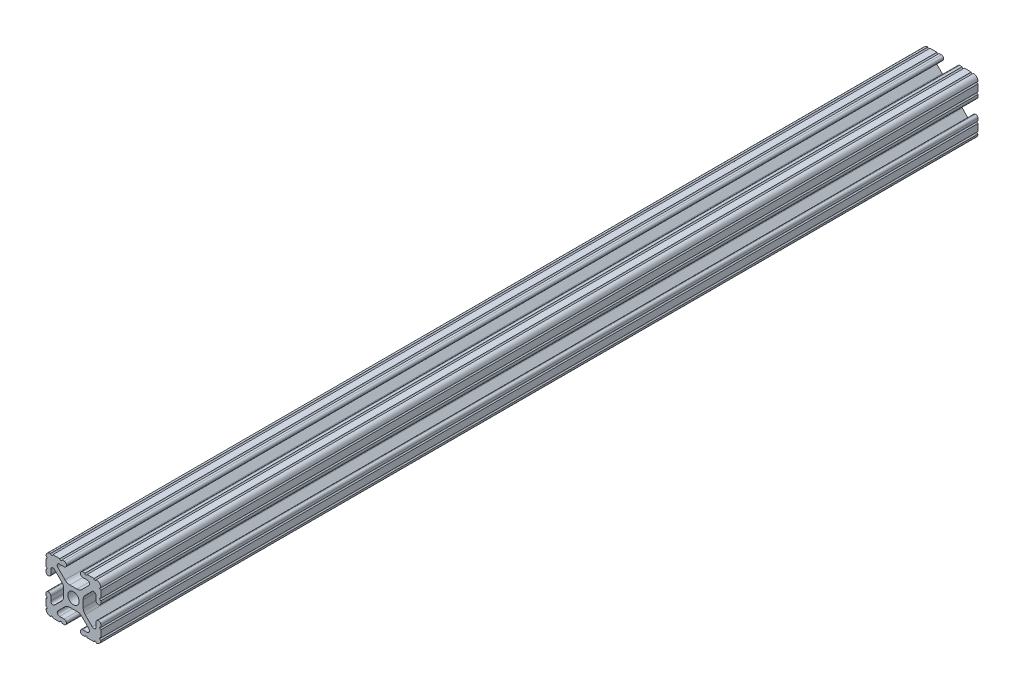
SolidWorks part; units mm, degrees
ref_plane "Front Plane" through (0, 0, 0) normal (0, 0, 1) x (1, 0, 0)
ref_plane "Top Plane" through (0, 0, 0) normal (0, 1, 0) x (1, 0, 0)
ref_plane "Right Plane" through (0, 0, 0) normal (1, 0, 0) x (0, 0, -1)
sketch "Sketch1" plane through (0, 0, 0) normal (0, 0, 1) x (1, 0, 0)
  line L0 (-7.207, 8.7244) -> (-3.8983, 5.4232)
  line L1 (-4.2875, 10.4902) -> (-6.4768, 10.4902)
  line L2 (-3.2385, 11.651) -> (-3.2385, 11.5392)
  line L3 (-5.3171, 12.7) -> (-4.2875, 12.7)
  line L4 (0, 13.4005) -> (0, -14.8534) construction
  line L5 (12.7, 0) -> (-13.9989, 0) construction
  line L6 (-9.5504, 12.7) -> (-6.3331, 12.7)
  line L7 (-12.7, 6.3331) -> (-12.7, 9.5504)
  line L8 (-12.7, 4.2875) -> (-12.7, 5.3171)
  line L9 (-11.5392, 3.2385) -> (-11.651, 3.2385)
  line L10 (-10.4902, 6.4021) -> (-10.4902, 4.2875)
  line L11 (-5.441, 3.8408) -> (-8.7371, 7.1294)
  line L12 (-4.5085, -1.5932) -> (-4.5085, 1.5932)
  line L13 (-1.7093, -4.4958) -> (1.7093, -4.4958)
  line L14 (3.9523, -5.4237) -> (7.1797, -8.6452)
  line L15 (6.4164, -10.4902) -> (4.2875, -10.4902)
  line L16 (3.2385, -11.5392) -> (3.2385, -11.651)
  line L17 (4.2875, -12.7) -> (5.3171, -12.7)
  line L18 (6.3331, -12.7) -> (9.5504, -12.7)
  line L19 (12.7, -9.5504) -> (12.7, -6.3331)
  line L20 (12.7, -5.3171) -> (12.7, -4.2875)
  line L21 (11.651, -3.2385) -> (11.5392, -3.2385)
  line L22 (10.4902, -4.2875) -> (10.4902, -6.4021)
  line L23 (8.7371, -7.1294) -> (5.441, -3.8408)
  line L24 (4.5085, -1.5932) -> (4.5085, 1.5932)
  line L25 (5.441, 3.8408) -> (8.7371, 7.1294)
  line L26 (10.4902, 6.4021) -> (10.4902, 4.2875)
  line L27 (11.5392, 3.2385) -> (11.651, 3.2385)
  line L28 (12.7, 4.2875) -> (12.7, 5.3171)
  line L29 (12.7, 6.3331) -> (12.7, 9.5504)
  line L30 (9.5504, 12.7) -> (6.3331, 12.7)
  line L31 (5.3171, 12.7) -> (4.2875, 12.7)
  line L32 (3.2385, 11.651) -> (3.2385, 11.5392)
  line L33 (4.2875, 10.4902) -> (6.4768, 10.4902)
  line L34 (7.207, 8.7244) -> (3.8983, 5.4232)
  line L35 (1.6558, 4.4958) -> (-1.6558, 4.4958)
  line L36 (-8.7371, -7.1294) -> (-5.441, -3.8408)
  line L37 (-10.4902, -4.2875) -> (-10.4902, -6.4021)
  line L38 (-11.651, -3.2385) -> (-11.5392, -3.2385)
  line L39 (-12.7, -5.3171) -> (-12.7, -4.2875)
  line L40 (-12.7, -9.5504) -> (-12.7, -6.3331)
  line L41 (-6.3331, -12.7) -> (-9.5504, -12.7)
  line L42 (-4.2875, -12.7) -> (-5.3171, -12.7)
  line L43 (-3.2385, -11.5392) -> (-3.2385, -11.651)
  line L44 (-6.4164, -10.4902) -> (-4.2875, -10.4902)
  line L45 (-3.9523, -5.4237) -> (-7.1797, -8.6452)
  arc A0 (-7.207, 8.7244) -> (-6.4768, 10.4902) centre (-6.4768, 9.4563) cw
  arc A1 (-3.2385, 11.5392) -> (-4.2875, 10.4902) centre (-4.2875, 11.5392) cw
  arc A2 (-4.2875, 12.7) -> (-3.2385, 11.651) centre (-4.2875, 11.651) cw
  arc A3 (-5.3171, 12.7) -> (-6.3331, 12.7) centre (-5.8251, 12.7) cw
  arc A4 (-9.5504, 12.7) -> (-10.5664, 12.6998) centre (-10.0584, 12.7) cw
  arc A5 (-12.6998, 10.5664) -> (-10.5664, 12.6998) centre (-10.5918, 10.5918) cw
  arc A6 (-12.6998, 10.5664) -> (-12.7, 9.5504) centre (-12.7, 10.0584) cw
  arc A7 (-12.7, 6.3331) -> (-12.7, 5.3171) centre (-12.7, 5.8251) cw
  arc A8 (-11.651, 3.2385) -> (-12.7, 4.2875) centre (-11.651, 4.2875) cw
  arc A9 (-10.4902, 4.2875) -> (-11.5392, 3.2385) centre (-11.5392, 4.2875) cw
  circle A10 centre (0, 0) radius 2.6035
  arc A11 (-10.4902, 6.4021) -> (-8.7371, 7.1294) centre (-9.4628, 6.4021) cw
  arc A12 (-5.441, 3.8408) -> (-4.5085, 1.5932) centre (-7.6835, 1.5932) cw
  arc A13 (-4.5085, -1.5932) -> (-5.441, -3.8408) centre (-7.6835, -1.5932) cw
  arc A14 (-8.7371, -7.1294) -> (-10.4902, -6.4021) centre (-9.4628, -6.4021) cw
  arc A15 (-1.7093, -4.4958) -> (-3.9523, -5.4237) centre (-1.7093, -7.6708) ccw
  arc A16 (3.9523, -5.4237) -> (1.7093, -4.4958) centre (1.7093, -7.6708) ccw
  arc A17 (6.4164, -10.4902) -> (7.1797, -8.6452) centre (6.4164, -9.4098) ccw
  arc A18 (4.2875, -10.4902) -> (3.2385, -11.5392) centre (4.2875, -11.5392) ccw
  arc A19 (3.2385, -11.651) -> (4.2875, -12.7) centre (4.2875, -11.651) ccw
  arc A20 (6.3331, -12.7) -> (5.3171, -12.7) centre (5.8251, -12.7) ccw
  arc A21 (10.5664, -12.6998) -> (9.5504, -12.7) centre (10.0584, -12.7) ccw
  arc A22 (10.5664, -12.6998) -> (12.6998, -10.5664) centre (10.5918, -10.5918) ccw
  arc A23 (12.7, -9.5504) -> (12.6998, -10.5664) centre (12.7, -10.0584) ccw
  arc A24 (12.7, -5.3171) -> (12.7, -6.3331) centre (12.7, -5.8251) ccw
  arc A25 (12.7, -4.2875) -> (11.651, -3.2385) centre (11.651, -4.2875) ccw
  arc A26 (11.5392, -3.2385) -> (10.4902, -4.2875) centre (11.5392, -4.2875) ccw
  arc A27 (8.7371, -7.1294) -> (10.4902, -6.4021) centre (9.4628, -6.4021) ccw
  arc A28 (4.5085, -1.5932) -> (5.441, -3.8408) centre (7.6835, -1.5932) ccw
  arc A29 (5.441, 3.8408) -> (4.5085, 1.5932) centre (7.6835, 1.5932) ccw
  arc A30 (10.4902, 6.4021) -> (8.7371, 7.1294) centre (9.4628, 6.4021) ccw
  arc A31 (10.4902, 4.2875) -> (11.5392, 3.2385) centre (11.5392, 4.2875) ccw
  arc A32 (11.651, 3.2385) -> (12.7, 4.2875) centre (11.651, 4.2875) ccw
  arc A33 (12.7, 6.3331) -> (12.7, 5.3171) centre (12.7, 5.8251) ccw
  arc A34 (12.6998, 10.5664) -> (12.7, 9.5504) centre (12.7, 10.0584) ccw
  arc A35 (12.6998, 10.5664) -> (10.5664, 12.6998) centre (10.5918, 10.5918) ccw
  arc A36 (9.5504, 12.7) -> (10.5664, 12.6998) centre (10.0584, 12.7) ccw
  arc A37 (5.3171, 12.7) -> (6.3331, 12.7) centre (5.8251, 12.7) ccw
  arc A38 (4.2875, 12.7) -> (3.2385, 11.651) centre (4.2875, 11.651) ccw
  arc A39 (3.2385, 11.5392) -> (4.2875, 10.4902) centre (4.2875, 11.5392) ccw
  arc A40 (7.207, 8.7244) -> (6.4768, 10.4902) centre (6.4768, 9.4563) ccw
  arc A41 (1.6558, 4.4958) -> (3.8983, 5.4232) centre (1.6558, 7.6708) ccw
  arc A42 (-1.6558, 4.4958) -> (-3.8983, 5.4232) centre (-1.6558, 7.6708) cw
  arc A43 (-11.5392, -3.2385) -> (-10.4902, -4.2875) centre (-11.5392, -4.2875) cw
  arc A44 (-12.7, -4.2875) -> (-11.651, -3.2385) centre (-11.651, -4.2875) cw
  arc A45 (-12.7, -5.3171) -> (-12.7, -6.3331) centre (-12.7, -5.8251) cw
  arc A46 (-12.7, -9.5504) -> (-12.6998, -10.5664) centre (-12.7, -10.0584) cw
  arc A47 (-10.5664, -12.6998) -> (-12.6998, -10.5664) centre (-10.5918, -10.5918) cw
  arc A48 (-10.5664, -12.6998) -> (-9.5504, -12.7) centre (-10.0584, -12.7) cw
  arc A49 (-6.3331, -12.7) -> (-5.3171, -12.7) centre (-5.8251, -12.7) cw
  arc A50 (-3.2385, -11.651) -> (-4.2875, -12.7) centre (-4.2875, -11.651) cw
  arc A51 (-4.2875, -10.4902) -> (-3.2385, -11.5392) centre (-4.2875, -11.5392) cw
  arc A52 (-6.4164, -10.4902) -> (-7.1797, -8.6452) centre (-6.4164, -9.4098) cw
  dimension "D1" = 5.207
  dimension "D9" = 14.859
  dimension "D2" = 25.4
  dimension "D3" = 12.7
  dimension "D4" = 6.477
  dimension "D5" = 8.2042
  dimension "D6" = 9.017
  dimension "D8" = 2.2098
  dimension "D10" = 2.2098
extrude "Extrude1" add sketch "Sketch1" against normal blind 406.4
